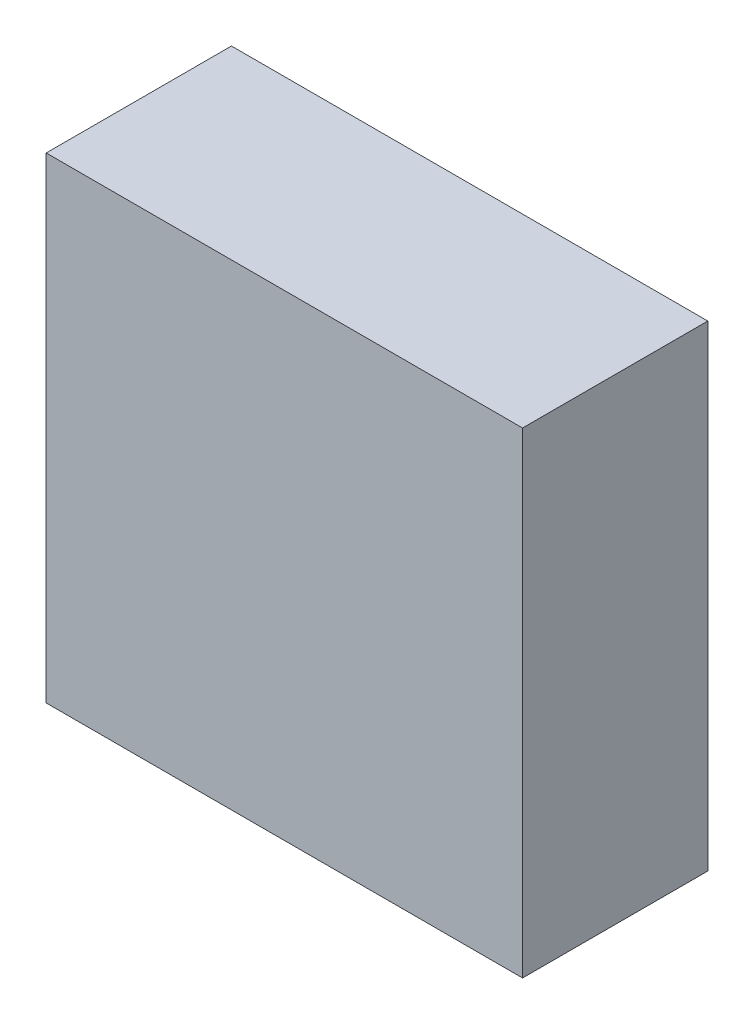
SolidWorks part; units mm, degrees
ref_plane "Přední rovina" through (0, 0, 0) normal (0, 0, 1) x (1, 0, 0)
ref_plane "Horní rovina" through (0, 0, 0) normal (0, 1, 0) x (1, 0, 0)
ref_plane "Pravá rovina" through (0, 0, 0) normal (1, 0, 0) x (0, 0, -1)
sketch "Skica1" plane through (0, 0, 0) normal (0, 0, 1) x (1, 0, 0)
  line L1 (0, 0) -> (90, 0)
  line L2 (0, 0) -> (0, -90)
  line L3 (0, -90) -> (90, -90)
  line L4 (90, 0) -> (90, -90)
  dimension "D1" = 90
extrude "Přidat vysunutím1" add sketch "Skica1" along normal blind 35
ref_plane "Rovina1" through (45, 0, 0) normal (-1, 0, 0) x (0, 0, 1)
ref_plane "Rovina2" through (0, -45, 0) normal (0, 1, 0) x (1, 0, 0)
